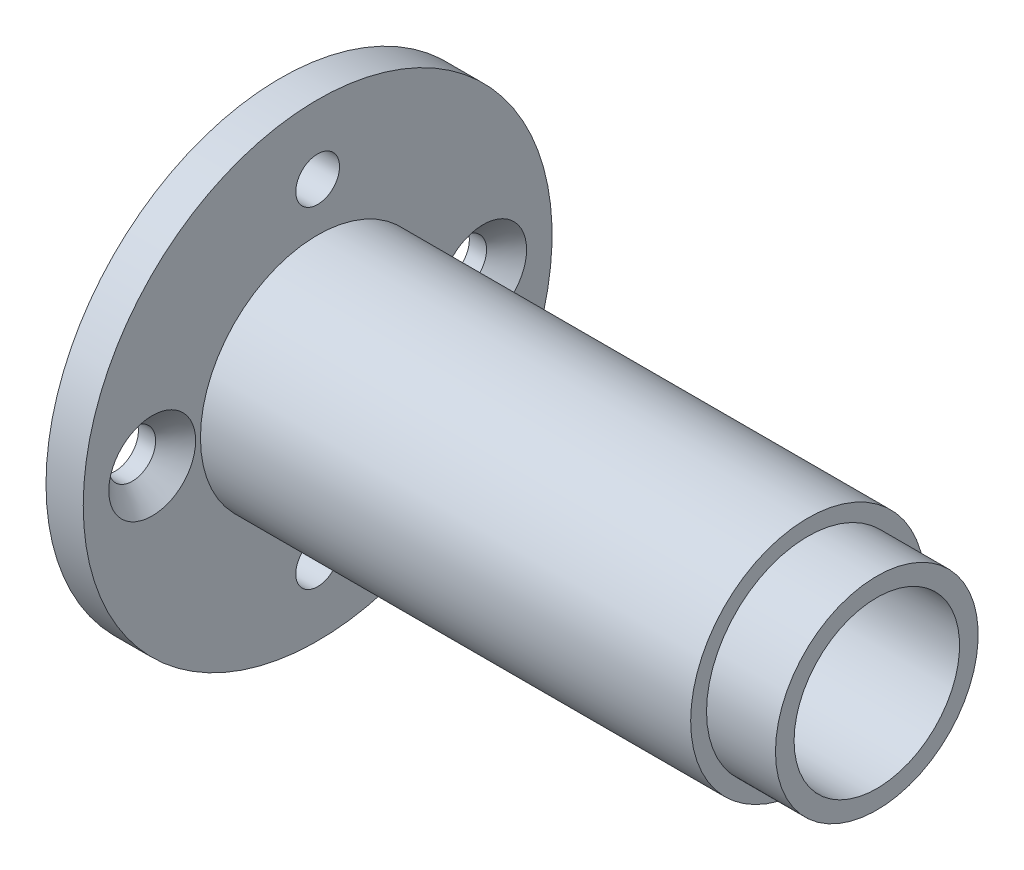
SolidWorks part; units mm, degrees
ref_plane "Front Plane" through (0, 0, 0) normal (0, 0, 1) x (1, 0, 0)
ref_plane "Top Plane" through (0, 0, 0) normal (0, 1, 0) x (1, 0, 0)
ref_plane "Right Plane" through (0, 0, 0) normal (1, 0, 0) x (0, 0, -1)
sketch "Sketch3" plane through (0, 0, 0) normal (0, 0, 1) x (1, 0, 0)
  line L0 (-58.5481, 189.9573) -> (284.033, 189.9573) construction
  line L2 (213.4012, -189.6279) -> (558.7345, -189.6279) construction
  line L4 (227.3705, -148.5737) -> (308.4812, -148.5737) construction
  line L41 (264.2584, -140.0737) -> (299.8084, -140.0737)
  line L42 (264.2584, -142.5737) -> (304.8084, -142.5737)
  line L43 (304.8084, -142.5737) -> (304.8084, -141.2237)
  line L44 (299.8084, -140.0737) -> (299.8084, -141.2237)
  line L45 (299.8084, -141.2237) -> (304.8084, -141.2237)
  line L48 (264.2584, -142.5737) -> (264.2584, -145.3237)
  line L55 (261.5584, -143.8237) -> (262.5584, -143.8237) construction
  line L56 (262.5584, -143.8237) -> (262.5584, -145.3237) construction
  line L58 (261.5584, -143.8237) -> (261.5584, -145.3237)
  line L59 (261.5584, -145.3237) -> (262.5584, -145.3237)
  line L61 (262.5584, -145.3237) -> (264.2584, -145.3237)
  line L94 (261.5584, -131.5737) -> (264.2584, -131.5737)
  line L97 (261.5584, -143.8237) -> (261.5584, -131.5737)
  line L112 (264.2584, -140.0737) -> (264.2584, -131.5737)
  dimension "D1" = 2.7
  dimension "D2" = 5
  dimension "D3" = 1.35
  dimension "D4" = 2.75
  dimension "D5" = 1.15
  dimension "D6" = 6
  dimension "D7" = 17
  dimension "D8" = 1.5
  dimension "D9" = 1
revolve "Revolve19" add sketch "Sketch3" angle 360 about L4
sketch "Sketch4" plane through (264.2584, 0, 0) normal (1, 0, 0) x (0, 0, -1)
  circle A0 centre (0, -148.5737) radius 12 construction
  circle A1 centre (0, -136.5737) radius 1.5875
  circle A2 centre (0, -160.5737) radius 1.5875
  dimension "D1" = 24
  dimension "D2" = 3.175
  dimension "D3" = 3.175
extrude "Cut-Extrude1" cut sketch "Sketch4" against normal up to next
hole_wizard "CSK for M3 Countersunk Flat Head Screw1" positions "Sketch11" profile "Sketch12" countersink size "M3" standard "ISO"
sketch "Sketch11" plane through (264.2584, 0, 0) normal (1, 0, 0) x (0, 0, -1)
  circle A0 centre (0, -148.5737) radius 12 construction
  point P0 (-12, -148.5737)
  point P4 (12, -148.5737)
sketch "Sketch12" plane through (264.2584, -148.5737, 12) normal (0, 1, 0) x (0, 0, -1)
  line L0 (0, 0) -> (0, 11.0215)
  line L1 (0, 11.0215) -> (1.7, 10)
  line L2 (1.7, 10) -> (1.7, 1.45)
  line L3 (1.7, 1.45) -> (3.15, 0)
  line L5 (3.15, 0) -> (0, 0)
  line L6 (-1.7, 1.45) -> (-3.15, 0) construction
  line L10 (0, 11.0215) -> (-1.7, 10) construction
  line L11 (0, -6.35) -> (0, 107.95) construction
  dimension "Hole Dia." = 3.4
  dimension "Hole Depth" = 10
  dimension "Near C'Sink Dia." = 6.3
  dimension "Near C'Sink Angle" = 90
  dimension "Drill Angle" = 118
sketch "Sketch13" [suppressed] plane through (261.5584, 0, 0) normal (-1, 0, 0) x (0, 0, 1)
  circle A0 centre (0, -148.5737) radius 6.35
  dimension "D1" = 12.7
extrude "Cut-Extrude2" [suppressed] cut sketch "Sketch13" against normal blind 1
sketch "Sketch14" plane through (264.2584, 0, 0) normal (1, 0, 0) x (0, 0, -1)
  line L0 (0, -148.5737) -> (-3.25, -148.5737) construction
  line L1 (0, -148.5737) -> (-2.8991, -151.4728) construction
  circle A0 centre (0, -148.5737) radius 3.25 construction
  circle A1 centre (-2.8991, -151.4728) radius 0.8
  dimension "D1" = 315
extrude "Cut-Extrude3" cut sketch "Sketch14" against normal blind 10
